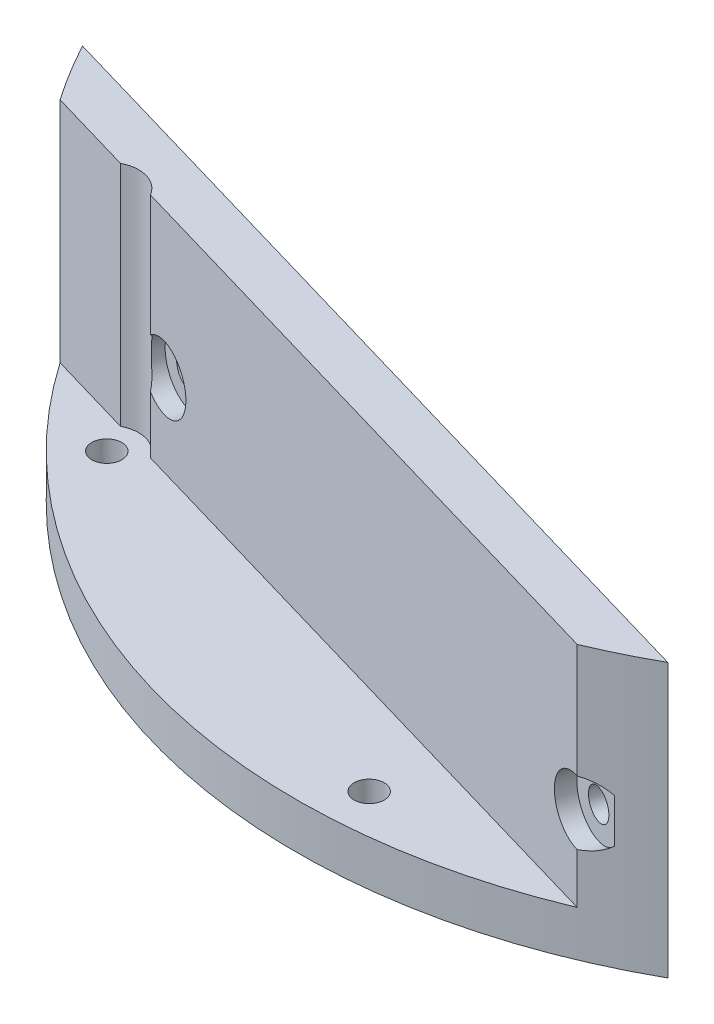
SolidWorks part; units mm, degrees
ref_plane "Front Plane" through (0, 0, 0) normal (0, 0, 1) x (1, 0, 0)
ref_plane "Top Plane" through (0, 0, 0) normal (0, 1, 0) x (1, 0, 0)
ref_plane "Right Plane" through (0, 0, 0) normal (1, 0, 0) x (0, 0, -1)
sketch "Sketch1" plane through (0, 0, 0) normal (0, 1, 0) x (1, 0, 0)
  line L0 (41.3804, -52.1206) -> (62.9195, 21.6805)
  line L1 (0, 0) -> (0, 66.55) construction
  line L2 (32.7481, -57.935) -> (-58.7697, -31.2253)
  line L3 (0, 0) -> (-47.058, -47.058) construction
  line L4 (0, 0) -> (0, -66.55) construction
  line L5 (0, 0) -> (3.483, -66.4588) construction
  circle A0 centre (0, 0) radius 66.55
  circle A2 centre (3.2213, -61.4656) radius 1.65
  circle A3 centre (-43.5224, -43.5224) radius 1.65
  dimension "D1" = 133.1
  dimension "D7" = 61.55
  dimension "D8" = 61.55
  dimension "D9" = 3.3
  dimension "D10" = 3.3
  dimension "D2" = 76.88
  dimension "D3" = 16.27
  dimension "D4" = 90
  dimension "D5" = 8
  dimension "D6" = 3
extrude "Boss-Extrude1" add sketch "Sketch1" along normal blind 5 contours L2 A0 A3 A2
sketch "Sketch2" plane through (0, 5, 0) normal (0, 1, 0) x (1, 0, 0)
  line L0 (-58.7697, -31.2253) -> (32.7481, -57.935)
  line L1 (-40.494, -41.7677) -> (26.121, -61.2095)
  line L2 (-54.9442, -37.5504) -> (-45.1316, -40.4143)
  arc A0 (26.121, -61.2095) -> (32.7481, -57.935) centre (0, 0) ccw
  arc A1 (-58.7697, -31.2253) -> (-54.9442, -37.5504) centre (0, 0) ccw
  arc A2 (-40.494, -41.7677) -> (-45.1316, -40.4143) centre (-43.5224, -43.5224) ccw
  dimension "D2" = 7
  dimension "D1" = 5
extrude "Boss-Extrude2" add sketch "Sketch2" along normal blind 25
sketch "Sketch3" plane through (-14.4116, 0, 49.3799) normal (-0.2802, 0, 0.96) x (0.96, 0, 0.2802)
  line L0 (42.2236, 30) -> (42.2236, 5) construction
  line L1 (47.6679, 0) -> (-47.6679, 0) construction
  circle A0 centre (41.5636, 14) radius 1.65
  circle A1 centre (-24.9364, 14) radius 1.65
  dimension "D1" = 0.66
  dimension "D2" = 3.3
  dimension "D3" = 3.3
  dimension "D4" = 14
  dimension "D5" = 14
  dimension "D6" = 67.16
extrude "Cut-Extrude1" cut sketch "Sketch3" against normal through all
sketch "Sketch4" plane through (-14.4116, 0, 49.3799) normal (-0.2802, 0, 0.96) x (0.96, 0, 0.2802)
  circle A0 centre (41.5636, 14) radius 3.5
  circle A1 centre (-24.9364, 14) radius 3.5
  dimension "D1" = 7
  dimension "D2" = 7
extrude "Cut-Extrude2" cut sketch "Sketch4" against normal blind 2
sketch "Sketch5" plane through (0, 0, 0) normal (0, -1, 0) x (1, 0, 0)
  circle A0 centre (0, 0) radius 66.25
  circle A3 centre (0, 0) radius 67.5
  dimension "D1" = 132.5
  dimension "D2" = 135
extrude "Cut-Extrude3" cut sketch "Sketch5" against normal through all
